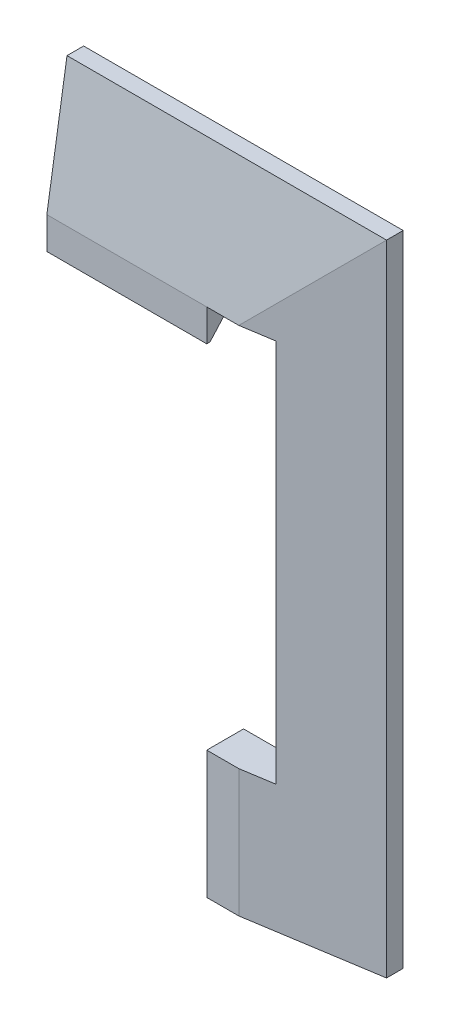
SolidWorks part; units mm, degrees
ref_plane "Płaszczyzna przednia" through (0, 0, 0) normal (0, 0, 1) x (1, 0, 0)
ref_plane "Płaszczyzna górna" through (0, 0, 0) normal (0, 1, 0) x (1, 0, 0)
ref_plane "Płaszczyzna prawa" through (0, 0, 0) normal (1, 0, 0) x (0, 0, -1)
sketch "Szkic2" plane through (0, 0, 0) normal (0, 0, 1) x (1, 0, 0)
  line L0 (18.5428, 83.2454) -> (18.5428, 43.3454)
  line L1 (-81.3572, 83.2454) -> (18.5428, 83.2454)
  line L2 (-81.3572, 83.2454) -> (-81.3572, -116.5546)
  line L3 (-81.3572, -116.5546) -> (18.5428, -116.5546)
  line L5 (-51.4572, 43.3454) -> (18.5428, 43.3454)
  line L6 (-51.4572, 43.3454) -> (-51.4572, -76.6546)
  line L7 (-51.4572, -76.6546) -> (18.5428, -76.6546)
  line L9 (-51.4572, -16.6546) -> (-81.3572, -16.6546) construction
  line L10 (18.5428, 43.3454) -> (18.5428, 83.2454) construction
  line L11 (18.5428, -76.6546) -> (18.5428, -116.5546) construction
  line L12 (18.5428, -76.6546) -> (18.5428, -116.5546)
  dimension "D1" = 199.8
  dimension "D3" = 120
  dimension "D4" = 29.9
extrude "Dodanie-wyciągnięcie1" add sketch "Szkic2" along normal blind 5.2
ref_plane "Płaszczyzna1" through (0, 0, 11.5) normal (0, 0, 1) x (1, 0, 0)
sketch "Szkic3" plane through (0, 0, 11.5) normal (0, 0, 1) x (1, 0, 0)
  line L5 (18.5428, -76.6546) -> (-51.4572, -76.6546) construction
  line L6 (-41.4572, -76.6546) -> (18.5428, -76.6546)
  line L12 (-41.4572, -76.6546) -> (-41.4572, 83.2454)
  line L13 (18.5428, 83.2454) -> (-81.3572, 83.2454) construction
  line L14 (-41.4572, 83.2454) -> (18.5428, 83.2454)
  line L15 (18.5428, 83.2454) -> (18.5428, -76.6546)
sketch "Szkic5" plane through (0, 0, 5.2) normal (0, 0, 1) x (1, 0, 0)
  line L1 (-81.3572, 83.2454) -> (18.5428, 83.2454)
  line L2 (-81.3572, 83.2454) -> (-81.3572, -116.5546)
  line L3 (-81.3572, -116.5546) -> (18.5428, -116.5546)
  line L4 (18.5428, 83.2454) -> (18.5428, -116.5546)
loft "Wyciągnięcie po profilach3" add profiles "Szkic3", "Szkic5"
sketch "Szkic6" plane through (-51.4572, 0, 0) normal (1, 0, 0) x (0, 0, -1)
  line L1 (0, 43.3454) -> (-49.2712, 43.3454)
  line L2 (0, 43.3454) -> (0, -76.6546)
  line L3 (0, -76.6546) -> (-49.2712, -76.6546)
  line L4 (-49.2712, 43.3454) -> (-49.2712, -76.6546)
extrude "Wytnij-wyciągnięcie1" cut sketch "Szkic6" along normal blind 78
sketch "Szkic7" plane through (-51.4572, 0, 0) normal (1, 0, 0) x (0, 0, -1)
  line L0 (-5.12, -76.6546) -> (-5.12, -36.5546) construction
  line L2 (-5.12, -36.5546) -> (-5.12, 3.2454) construction
  line L3 (-5.12, 3.2454) -> (-5.12, 43.3454) construction
  line L5 (0, -76.6546) -> (0, 43.3454) construction
  line L7 (-5.12, -34.1298) -> (-7.22, -35.3422)
  line L8 (-7.22, -35.3422) -> (-7.22, -37.7671)
  line L9 (-7.22, -37.7671) -> (-5.12, -38.9795)
  line L10 (-5.12, -38.9795) -> (-3.02, -37.7671)
  line L11 (-3.02, -37.7671) -> (-3.02, -35.3422)
  line L12 (-3.02, -35.3422) -> (-5.12, -34.1298)
  line L13 (-5.12, 5.6702) -> (-7.22, 4.4578)
  line L14 (-7.22, 4.4578) -> (-7.22, 2.0329)
  line L15 (-7.22, 2.0329) -> (-5.12, 0.8205)
  line L16 (-5.12, 0.8205) -> (-3.02, 2.0329)
  line L17 (-3.02, 2.0329) -> (-3.02, 4.4578)
  line L18 (-3.02, 4.4578) -> (-5.12, 5.6702)
  circle A0 centre (-5.12, -36.5546) radius 2.1 construction
  circle A1 centre (-5.12, 3.2454) radius 2.1 construction
  dimension "D2" = 4.2
  dimension "D3" = 4.2
  dimension "D1" = 5.12
extrude "Wytnij-wyciągnięcie2" cut sketch "Szkic7" against normal blind 5.6
sketch "Szkic9" plane through (-51.4572, 0, 0) normal (1, 0, 0) x (0, 0, -1)
  circle A0 centre (-5.12, 3.2454) radius 2.4249
  circle A1 centre (-5.12, -36.5546) radius 2.4249
  circle A2 centre (-5.12, 3.2454) radius 1.2
  circle A3 centre (-5.12, -36.5546) radius 1.2
extrude "Dodanie-wyciągnięcie3" add sketch "Szkic9" against normal blind 3.8
sketch "Szkic10" plane through (0, 0, 11.5) normal (0, 0, 1) x (1, 0, 0)
  line L0 (-41.4572, 83.2454) -> (-41.4572, 43.3454) construction
  line L1 (-31.4572, 83.2454) -> (18.5428, 83.2454)
  line L2 (-31.4572, 83.2454) -> (-31.4572, 43.3454)
  line L3 (-31.4572, 43.3454) -> (18.5428, 43.3454)
  line L4 (18.5428, 83.2454) -> (18.5428, 43.3454)
  dimension "D1" = 10
extrude "Wytnij-wyciągnięcie4" cut sketch "Szkic10" against normal blind 24
mirror "Lustro1" about plane through (18.5428, 83.2454, 5.2) normal (-1, 0, 0) of bodies 128
move or copy body "Obiekt-Przenieś/Kopiuj1" bodies to move or copy 129 copy no translate (34.8901, 0, 0) parameters "D1"=34.8901, "D2"=0, "D3"=0
delete or keep bodies "Obiekt-Usuń/zachowaj 1" type delete bodies bodies 128
sketch "Szkic11" plane through (53.433, 0, 0) normal (-1, 0, 0) x (0, 0, 1)
  line L0 (11.5, -76.6546) -> (1.5, -76.6546)
  line L1 (9.9211, -76.6546) -> (0, -76.6546) construction
  line L2 (1.5, -76.6546) -> (10.5, -66.6546)
  line L3 (10.5, -66.6546) -> (11.5, -66.6546)
  line L4 (11.5, -66.6546) -> (11.5, -76.6546)
extrude "Dodanie-wyciągnięcie4" add sketch "Szkic11" against normal blind 50
mirror "Lustro2" about plane through (153.333, 83.2454, 5.2) normal (0, -1, 0) of bodies 131
delete or keep bodies "Obiekt-Usuń/zachowaj 2" type delete bodies bodies 131
